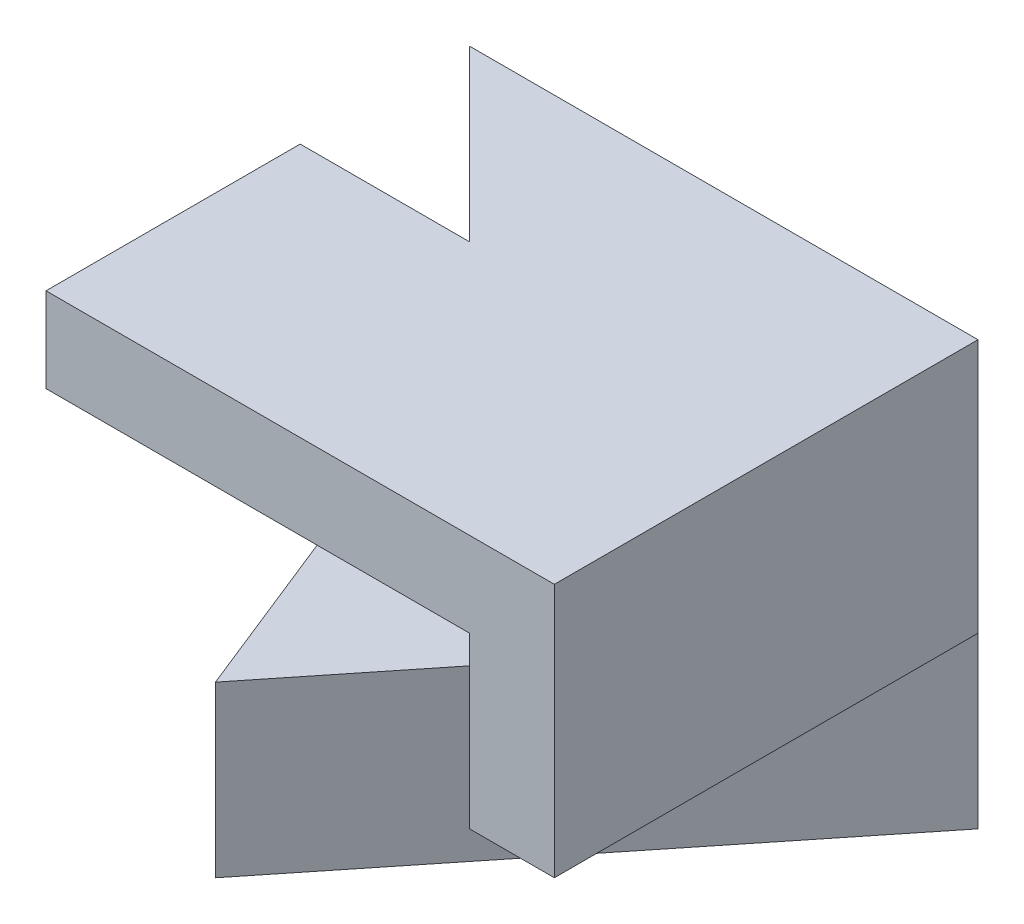
SolidWorks part; units mm, degrees
ref_plane "Front Plane" through (0, 0, 0) normal (0, 0, 1) x (1, 0, 0)
ref_plane "Top Plane" through (0, 0, 0) normal (0, 1, 0) x (1, 0, 0)
ref_plane "Right Plane" through (0, 0, 0) normal (1, 0, 0) x (0, 0, -1)
sketch "Sketch3" plane through (0, 0, 0) normal (0, 0, 1) x (1, 0, 0)
  line L1 (0, 0) -> (6, 0)
  line L2 (0, 0) -> (0, 5)
  line L3 (0, 5) -> (6, 5)
  line L4 (6, 0) -> (6, 5)
  dimension "D1" = 6
  dimension "D2" = 5
extrude "Boss-Extrude1" add sketch "Sketch3" along normal blind 5
sketch "Sketch4" plane through (0, 5, 0) normal (0, 1, 0) x (1, 0, 0)
  line L0 (0, 0) -> (5, -5)
  line L1 (6, -5) -> (0, -5) construction
  line L2 (5, -5) -> (0, -5)
  line L3 (0, -5) -> (0, 0)
  dimension "D1" = 5
extrude "Cut-Extrude1" cut sketch "Sketch4" against normal blind 3
sketch "Sketch5" plane through (0, 2, 0) normal (0, 1, 0) x (1, 0, 0)
  line L0 (0, 0) -> (2, -5)
  line L1 (0, -5) -> (5, -5) construction
  line L2 (2, -5) -> (0, -5)
  line L3 (0, -5) -> (0, 0)
  dimension "D1" = 2
extrude "Cut-Extrude2" cut sketch "Sketch5" against normal blind 3
sketch "Sketch6" plane through (6, 0, 0) normal (1, 0, 0) x (0, 0, -1)
  line L1 (-5, 5) -> (-2, 5)
  line L2 (-5, 5) -> (-5, 4)
  line L3 (-5, 4) -> (-2, 4)
  line L4 (-2, 5) -> (-2, 4)
  dimension "D1" = 3
  dimension "D2" = 1
extrude "Boss-Extrude2" add sketch "Sketch6" against normal blind 6
sketch "Sketch7" plane through (0, 0, 0) normal (0, -1, 0) x (1, 0, 0)
  line L0 (2, 5) -> (6, 0)
  line L1 (6, 0) -> (6, 5)
  line L2 (6, 5) -> (2, 5)
extrude "Cut-Extrude3" cut sketch "Sketch7" against normal blind 2
